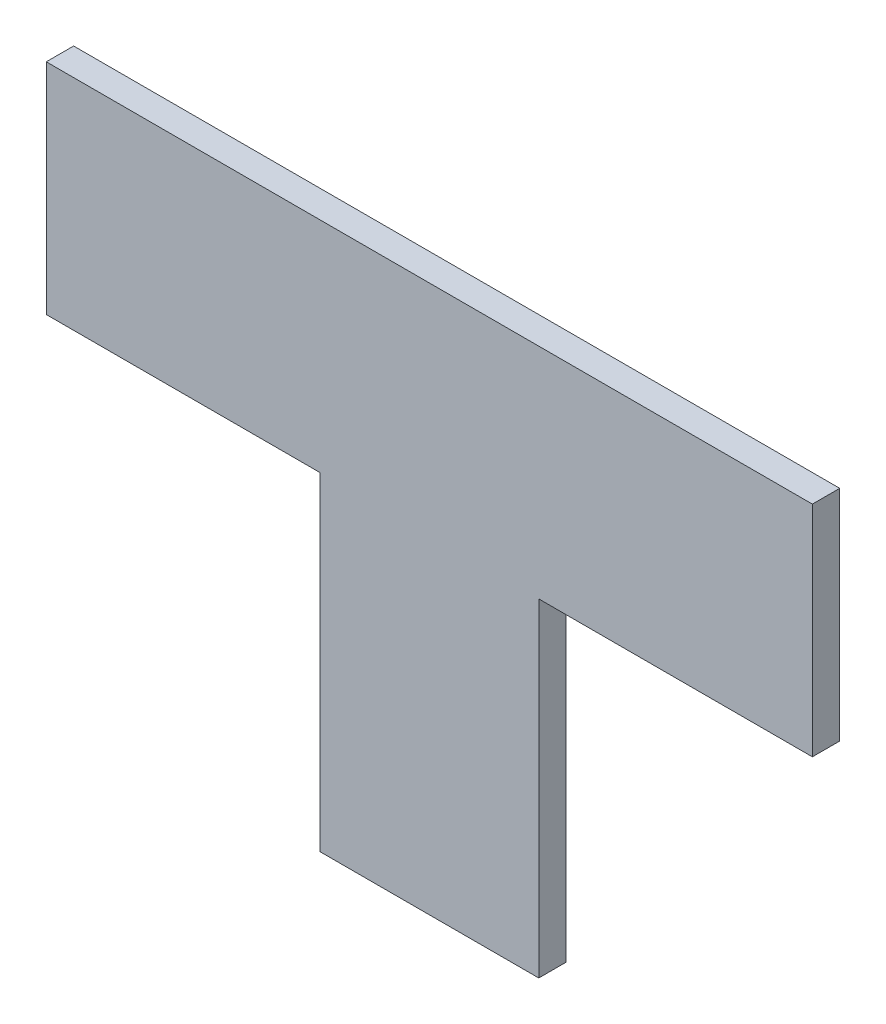
SolidWorks part; units mm, degrees
ref_plane "Front Plane" through (0, 0, 0) normal (0, 0, 1) x (1, 0, 0)
ref_plane "Top Plane" through (0, 0, 0) normal (0, 1, 0) x (1, 0, 0)
ref_plane "Right Plane" through (0, 0, 0) normal (1, 0, 0) x (0, 0, -1)
sketch "Sketch1" plane through (0, 0, 0) normal (0, 0, 1) x (1, 0, 0)
  line L0 (0, 0) -> (0, 38.1)
  line L1 (0, 38.1) -> (-31.75, 38.1)
  line L2 (-31.75, 38.1) -> (-31.75, 63.5)
  line L3 (-31.75, 63.5) -> (57.15, 63.5)
  line L4 (57.15, 63.5) -> (57.15, 38.1)
  line L5 (57.15, 38.1) -> (25.4, 38.1)
  line L6 (25.4, 38.1) -> (25.4, 0)
  line L7 (25.4, 0) -> (0, 0)
  dimension "D1" = 38.1
  dimension "D2" = 88.9
  dimension "D3" = 25.4
extrude "Boss-Extrude1" add sketch "Sketch1" along normal blind 3.175
